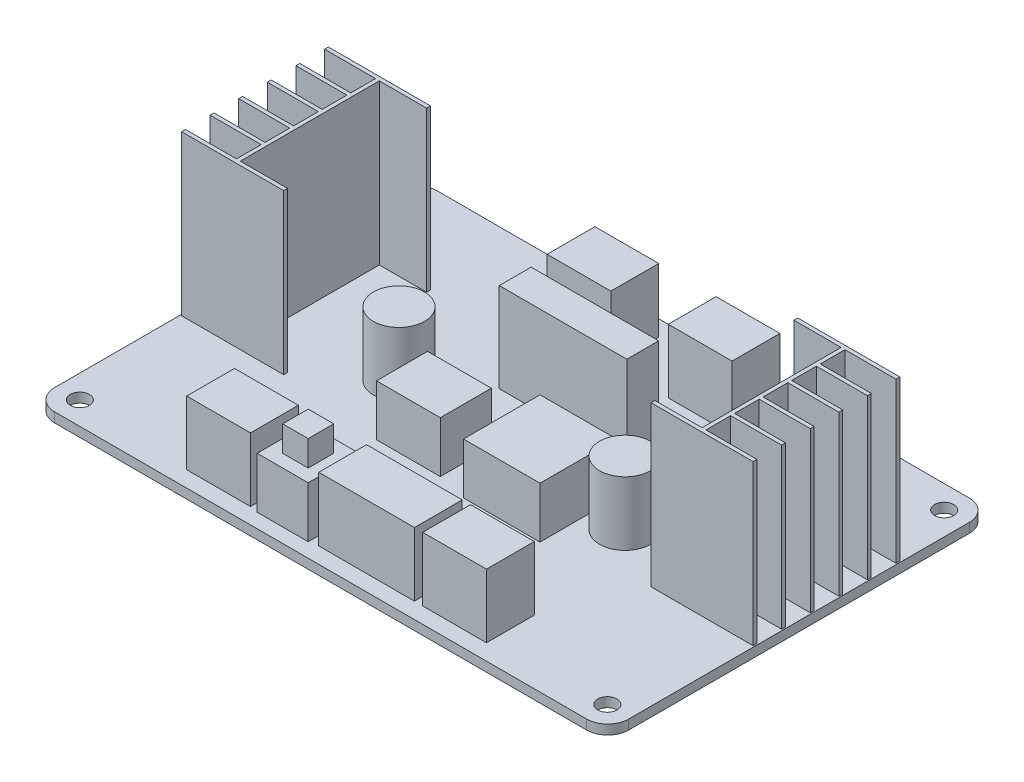
SolidWorks part; units mm, degrees
ref_plane "前视基准面" through (0, 0, 0) normal (0, 0, 1) x (1, 0, 0)
ref_plane "上视基准面" through (0, 0, 0) normal (0, 1, 0) x (1, 0, 0)
ref_plane "右视基准面" through (0, 0, 0) normal (1, 0, 0) x (0, 0, -1)
sketch "草图1" plane through (0, 0, 0) normal (0, 1, 0) x (1, 0, 0)
  line L0 (0, -67.2816) -> (0, 67.2816) construction
  line L1 (-41.7, 30) -> (41.7, 30)
  line L2 (-45, 26.7) -> (-45, -26.7)
  line L3 (-41.7, -30) -> (41.7, -30)
  line L4 (45, 26.7) -> (45, -26.7)
  line L5 (-45, 30) -> (45, -30) construction
  line L6 (-45, -30) -> (45, 30) construction
  line L7 (-88.3495, 0) -> (88.3495, 0) construction
  circle A0 centre (-41.35, 26.4) radius 1.5
  circle A1 centre (41.35, 26.4) radius 1.5
  circle A2 centre (41.35, -26.4) radius 1.5
  circle A3 centre (-41.35, -26.4) radius 1.5
  arc A4 (-45, -26.7) -> (-41.7, -30) centre (-41.7, -26.7) ccw
  arc A5 (45, -26.7) -> (41.7, -30) centre (41.7, -26.7) cw
  arc A6 (41.7, 30) -> (45, 26.7) centre (41.7, 26.7) cw
  arc A7 (-41.7, 30) -> (-45, 26.7) centre (-41.7, 26.7) ccw
  point P0 (0, 0)
  point P9 (0, 0)
  point P12 (0, 0)
  dimension "D3" = 3
  dimension "D4" = 82.7
  dimension "D5" = 52.8
  dimension "D6" = 3.3
  dimension "D1" = 60
  dimension "D2" = 90
extrude "凸台-拉伸1" add sketch "草图1" along normal blind 1.5
sketch "草图2" plane through (0, 1.5, 0) normal (0, 1, 0) x (1, 0, 0)
  line L0 (0, 54.0768) -> (0, -54.0768) construction
  line L1 (23.5, -27.5) -> (13.5, -27.5)
  line L2 (23.5, -27.5) -> (23.5, -20)
  line L3 (23.5, -20) -> (13.5, -20)
  line L4 (13.5, -27.5) -> (13.5, -20)
  line L5 (-41.7, -30) -> (41.7, -30) construction
  line L6 (41.7, 30) -> (-41.7, 30) construction
  line L7 (-4.5, 27.5) -> (-4.5, 20)
  line L8 (-14.5, 20) -> (-4.5, 20)
  line L9 (14.5, 27.5) -> (4.5, 27.5)
  line L10 (14.5, 27.5) -> (14.5, 20)
  line L11 (14.5, 20) -> (4.5, 20)
  line L12 (4.5, 27.5) -> (4.5, 20)
  line L13 (-14.5, 27.5) -> (-14.5, 20)
  line L14 (-14.5, 27.5) -> (-4.5, 27.5)
  line L15 (-13.5, -27.5) -> (-13.5, -20)
  line L16 (-23.5, -20) -> (-13.5, -20)
  line L17 (-23.5, -27.5) -> (-23.5, -20)
  line L18 (-23.5, -27.5) -> (-13.5, -27.5)
  point P7 (0, 0)
  dimension "D1" = 10
  dimension "D2" = 7.5
  dimension "D3" = 2.5
  dimension "D4" = 2.5
  dimension "D5" = 47
  dimension "D6" = 29
extrude "凸台-拉伸2" add sketch "草图2" along normal blind 10
sketch "草图3" plane through (0, 1.5, 0) normal (0, 1, 0) x (1, 0, 0)
  line L0 (-41.7, -30) -> (41.7, -30) construction
  line L1 (-4.2, -27.75) -> (-12.2, -27.75)
  line L2 (-4.2, -27.75) -> (-4.2, -19.75)
  line L3 (-4.2, -19.75) -> (-12.2, -19.75)
  line L4 (-12.2, -27.75) -> (-12.2, -19.75)
  line L5 (-13.5, -27.5) -> (-13.5, -20) construction
  dimension "D1" = 2.25
  dimension "D2" = 8
  dimension "D3" = 8
  dimension "D4" = 1.3
extrude "凸台-拉伸3" add sketch "草图3" along normal blind 8
sketch "草图4" plane through (0, 1.5, 0) normal (0, 1, 0) x (1, 0, 0)
  line L0 (-41.7, -30) -> (41.7, -30) construction
  line L1 (12.2, -27.5) -> (-2.8, -27.5)
  line L2 (12.2, -27.5) -> (12.2, -20)
  line L3 (12.2, -20) -> (-2.8, -20)
  line L4 (-2.8, -27.5) -> (-2.8, -20)
  line L5 (13.5, -20) -> (13.5, -27.5) construction
  dimension "D1" = 15
  dimension "D2" = 7.5
  dimension "D3" = 2.5
  dimension "D4" = 1.3
extrude "凸台-拉伸4" add sketch "草图4" along normal blind 10
sketch "草图5" plane through (0, 1.5, 0) normal (0, 1, 0) x (1, 0, 0)
  line L0 (0, 75.8424) -> (0, -75.8424) construction
  line L1 (44.8, 16) -> (28.8, 16)
  line L2 (28.8, 16) -> (28.8, 15.4)
  line L3 (28.8, 15.4) -> (36.2, 15.4)
  line L4 (36.2, 15.4) -> (36.2, -6.4)
  line L5 (36.2, -6.4) -> (28.8, -6.4)
  line L6 (28.8, -6.4) -> (28.8, -7)
  line L7 (28.8, -7) -> (44.8, -7)
  line L8 (44.8, -7) -> (44.8, -6.4)
  line L9 (44.8, -6.4) -> (36.8, -6.4)
  line L10 (36.8, -6.4) -> (36.8, -2.52)
  line L11 (36.8, -2.52) -> (44.8, -2.52)
  line L12 (44.8, -2.52) -> (44.8, -1.92)
  line L13 (44.8, -1.92) -> (36.8, -1.92)
  line L14 (36.8, -1.92) -> (36.8, 1.96)
  line L15 (36.8, 1.96) -> (44.8, 1.96)
  line L16 (44.8, 1.96) -> (44.8, 2.56)
  line L17 (44.8, 2.56) -> (36.8, 2.56)
  line L18 (36.8, 2.56) -> (36.8, 6.44)
  line L19 (36.8, 6.44) -> (44.8, 6.44)
  line L20 (44.8, 6.44) -> (44.8, 7.04)
  line L21 (44.8, 7.04) -> (36.8, 7.04)
  line L22 (36.8, 7.04) -> (36.8, 10.92)
  line L23 (36.8, 10.92) -> (44.8, 10.92)
  line L24 (44.8, 10.92) -> (44.8, 11.52)
  line L25 (44.8, 11.52) -> (36.8, 11.52)
  line L26 (36.8, 11.52) -> (36.8, 15.4)
  line L27 (36.8, 15.4) -> (44.8, 15.4)
  line L28 (44.8, 15.4) -> (44.8, 16)
  line L29 (41.7, 30) -> (-41.7, 30) construction
  line L30 (45, -26.7) -> (45, 26.7) construction
  line L31 (-44.8, 15.4) -> (-44.8, 16)
  line L32 (-36.8, 15.4) -> (-44.8, 15.4)
  line L33 (-36.8, 11.52) -> (-36.8, 15.4)
  line L34 (-44.8, 11.52) -> (-36.8, 11.52)
  line L35 (-44.8, 10.92) -> (-44.8, 11.52)
  line L36 (-36.8, 10.92) -> (-44.8, 10.92)
  line L37 (-36.8, 7.04) -> (-36.8, 10.92)
  line L38 (-44.8, 7.04) -> (-36.8, 7.04)
  line L39 (-44.8, 6.44) -> (-44.8, 7.04)
  line L40 (-36.8, 6.44) -> (-44.8, 6.44)
  line L41 (-36.8, 2.56) -> (-36.8, 6.44)
  line L42 (-44.8, 2.56) -> (-36.8, 2.56)
  line L43 (-44.8, 1.96) -> (-44.8, 2.56)
  line L44 (-36.8, 1.96) -> (-44.8, 1.96)
  line L45 (-36.8, -1.92) -> (-36.8, 1.96)
  line L46 (-44.8, -1.92) -> (-36.8, -1.92)
  line L47 (-44.8, -2.52) -> (-44.8, -1.92)
  line L48 (-36.8, -2.52) -> (-44.8, -2.52)
  line L49 (-36.8, -6.4) -> (-36.8, -2.52)
  line L50 (-44.8, -6.4) -> (-36.8, -6.4)
  line L51 (-44.8, -7) -> (-44.8, -6.4)
  line L52 (-28.8, -7) -> (-44.8, -7)
  line L53 (-28.8, -6.4) -> (-28.8, -7)
  line L54 (-36.2, -6.4) -> (-28.8, -6.4)
  line L55 (-36.2, 15.4) -> (-36.2, -6.4)
  line L56 (-28.8, 15.4) -> (-36.2, 15.4)
  line L57 (-28.8, 16) -> (-28.8, 15.4)
  line L58 (-44.8, 16) -> (-28.8, 16)
  point P4 (0, 0)
  dimension "D1" = 23
  dimension "D2" = 0.6
  dimension "D3" = 0.6
  dimension "D4" = 16
  dimension "D5" = 8
  dimension "D6" = 14
  dimension "D7" = 0.2
extrude "凸台-拉伸5" add sketch "草图5" along normal blind 25
sketch "草图6" plane through (0, 9.5, 0) normal (0, 1, 0) x (1, 0, 0)
  line L0 (-4.2, -19.75) -> (-12.2, -19.75) construction
  line L1 (-10.2, -21.75) -> (-6.2, -21.75)
  line L2 (-10.2, -21.75) -> (-10.2, -25.75)
  line L3 (-10.2, -25.75) -> (-6.2, -25.75)
  line L4 (-6.2, -21.75) -> (-6.2, -25.75)
  line L5 (-10.2, -21.75) -> (-6.2, -25.75) construction
  line L6 (-10.2, -25.75) -> (-6.2, -21.75) construction
  line L7 (-12.2, -19.75) -> (-12.2, -27.75) construction
  point P0 (-8.2, -23.75)
  point P5 (-8.2, -19.75)
  dimension "D1" = 4
  dimension "D2" = 4
  dimension "D3" = 2
  dimension "D4" = 2
extrude "凸台-拉伸6" add sketch "草图6" along normal blind 4
sketch "草图7" plane through (0, 1.5, 0) normal (0, 1, 0) x (1, 0, 0)
  line L0 (0, 0) -> (0, -34.8252) construction
  line L2 (-10, 13) -> (10, 13)
  line L3 (-10, 13) -> (-10, 8)
  line L4 (-10, 8) -> (10, 8)
  line L5 (10, 13) -> (10, 8)
  line L6 (-10, 13) -> (10, 8) construction
  line L7 (-10, 8) -> (10, 13) construction
  line L8 (12.2, -20) -> (-2.8, -20) construction
  point P3 (0, 10.5)
  dimension "D1" = 20
  dimension "D2" = 5
  dimension "D3" = 28
extrude "凸台-拉伸7" add sketch "草图7" along normal blind 14
sketch "草图8" plane through (0, 1.5, 0) normal (0, 1, 0) x (1, 0, 0)
  line L1 (14.025, -9.6332) -> (2.025, -9.6332)
  line L2 (14.025, -9.6332) -> (14.025, 2.3668)
  line L3 (14.025, 2.3668) -> (2.025, 2.3668)
  line L4 (2.025, -9.6332) -> (2.025, 2.3668)
  line L5 (-2.6844, -8.5556) -> (-12.6844, -8.5556)
  line L6 (-2.6844, -8.5556) -> (-2.6844, -0.5556)
  line L7 (-2.6844, -0.5556) -> (-12.6844, -0.5556)
  line L8 (-12.6844, -8.5556) -> (-12.6844, -0.5556)
  dimension "D1" = 12
  dimension "D2" = 12
  dimension "D3" = 10
  dimension "D4" = 8
extrude "凸台-拉伸8" add sketch "草图8" along normal blind 8
sketch "草图9" plane through (0, 1.5, 0) normal (0, 1, 0) x (1, 0, 0)
  line L0 (-87.3332, 5.8614) -> (87.3332, -5.8614) construction
  circle A0 centre (-19, 1.2752) radius 4
  circle A1 centre (19, -1.2752) radius 4
  point P4 (0, 0)
  dimension "D1" = 8
  dimension "D2" = 8
  dimension "D3" = 19
  dimension "D4" = 19
extrude "凸台-拉伸9" add sketch "草图9" along normal blind 10
